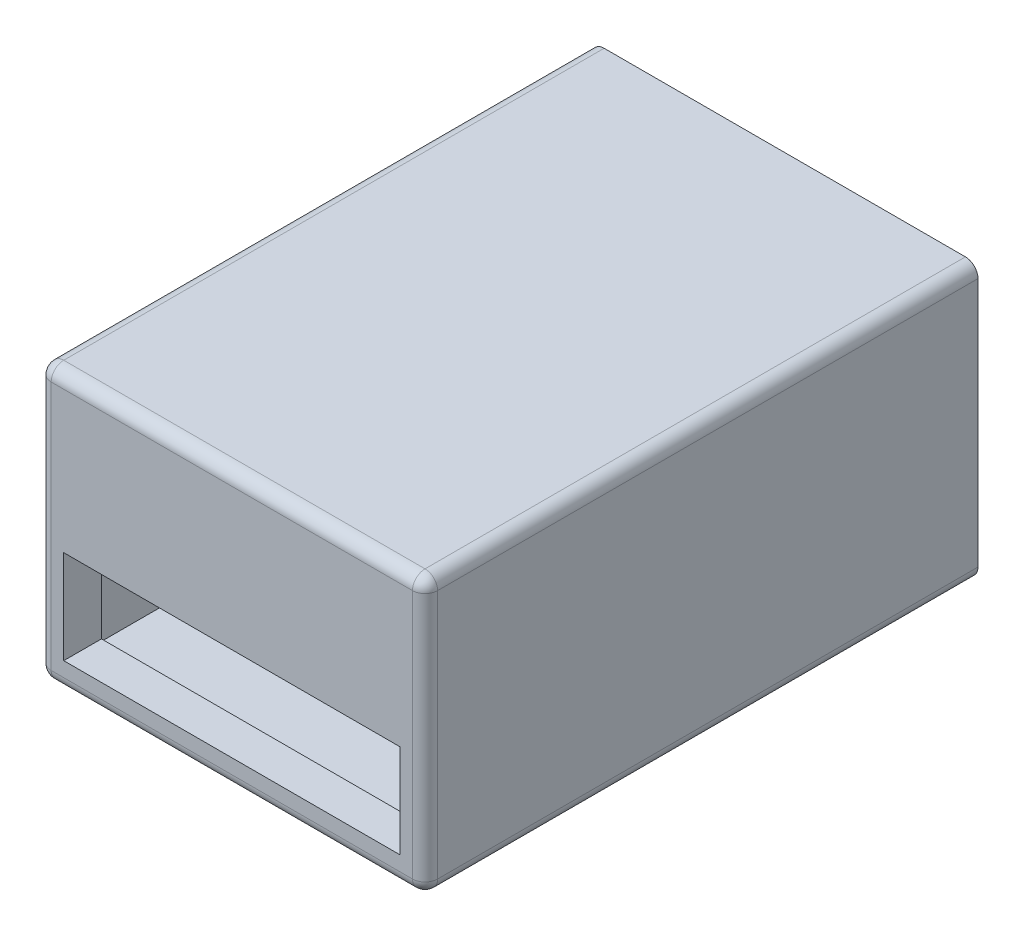
SolidWorks part; units mm, degrees
ref_plane "Plan de face" through (0, 0, 0) normal (0, 0, 1) x (1, 0, 0)
ref_plane "Plan de dessus" through (0, 0, 0) normal (0, 1, 0) x (1, 0, 0)
ref_plane "Plan de droite" through (0, 0, 0) normal (1, 0, 0) x (0, 0, -1)
sketch "Esquisse1" plane through (0, 0, 0) normal (0, 0, 1) x (1, 0, 0)
  line L1 (-31.6005, 34.6263) -> (29.8995, 34.6263)
  line L2 (-31.6005, 34.6263) -> (-31.6005, -9.1237)
  line L3 (-31.6005, -9.1237) -> (29.8995, -9.1237)
  line L4 (29.8995, 34.6263) -> (29.8995, -9.1237)
  dimension "D1" = 43.75
  dimension "D2" = 61.5
extrude "Boss.-Extru.1" add sketch "Esquisse1" along normal blind 88
sketch "Esquisse2" plane through (0, 34.6263, 0) normal (0, 1, 0) x (1, 0, 0)
  line L0 (29.8995, -88) -> (-31.6005, -88) construction
  line L1 (25.8995, -15) -> (-27.6005, -15)
  line L2 (25.8995, -15) -> (25.8995, -84)
  line L3 (25.8995, -84) -> (-27.6005, -84)
  line L4 (-27.6005, -15) -> (-27.6005, -84)
  line L5 (29.8995, -88) -> (29.8995, 0) construction
  dimension "D1" = 69
  dimension "D2" = 53.5
  dimension "D3" = 4
  dimension "D4" = 4
sketch "Esquisse3" plane through (0, 0, 88) normal (0, 0, 1) x (1, 0, 0)
  line L0 (-31.6005, -9.1237) -> (29.8995, -9.1237) construction
  line L1 (-27.6005, -5.1237) -> (25.8995, -5.1237)
  line L3 (-27.6005, 30.6263) -> (25.8995, 30.6263)
  line L17 (-27.6005, -4.7816) -> (25.8995, -4.7816)
  line L21 (-27.6005, -4.7816) -> (-27.6005, 10.1082)
  line L22 (-27.6005, 10.1082) -> (25.8995, 10.1082)
  line L23 (25.8995, 10.1082) -> (25.8995, -4.7816)
  dimension "D1" = 53.5
  dimension "D2" = 35.75
  dimension "D3" = 4
extrude "Enlèv. mat.-Extru.4" cut sketch "Esquisse3" against normal up to next
sketch "Esquisse6" plane through (0, 0, 0) normal (0, 0, -1) x (-1, 0, 0)
  line L7 (29.6005, 32.6263) -> (29.6005, -7.1237)
  line L8 (31.6005, 34.6263) -> (31.6005, -9.1237) construction
  line L10 (-29.8995, 34.6263) -> (31.6005, 34.6263) construction
  line L12 (31.6005, -9.1237) -> (-29.8995, -9.1237) construction
  line L13 (-27.9021, 32.6263) -> (29.6005, 32.6263)
  line L14 (-27.9021, 32.6263) -> (-27.9021, -7.1237)
  line L15 (-27.9021, -7.1237) -> (29.6005, -7.1237)
  line L18 (-29.8995, -9.1237) -> (-29.8995, 34.6263) construction
  dimension "D1" = 2
  dimension "D2" = 2
  dimension "D3" = 2
  dimension "D4" = 2
  dimension "D5" = 2
  dimension "D6" = 1.9974
  dimension "D7" = 2
extrude "Enlèv. mat.-Extru.5" cut sketch "Esquisse6" against normal blind 82
fillet "Congé4" radius 2 8 edges at (-31.6005, 34.6263, 44) (-31.6005, -9.1237, 44) (-31.6005, 12.7513, 88) (-0.8505, -9.1237, 88) (29.8995, -9.1237, 44) (29.8995, 12.7513, 88) (-0.8505, 34.6263, 88) (29.8995, 34.6263, 44)
sketch "Esquisse7" plane through (0, -7.1237, 0) normal (0, 1, 0) x (1, 0, 0)
  line L0 (27.9021, -82) -> (27.9021, 0) construction
  line L1 (27.9021, 0) -> (-29.6005, 0) construction
  circle A0 centre (18.0021, -9.4) radius 1.5
  dimension "D2" = 9.4
  dimension "D1" = 9.9
extrude "Boss.-Extru.2" add sketch "Esquisse7" along normal blind 5.2
sketch "Esquisse8" plane through (0, -7.1237, 0) normal (0, 1, 0) x (1, 0, 0)
  line L0 (-29.6005, -82) -> (-29.6005, 0) construction
  line L1 (27.9021, 0) -> (-29.6005, 0) construction
  circle A0 centre (-9.8505, -9.5) radius 1.5
  dimension "D1" = 19.75
  dimension "D2" = 9.5
extrude "Boss.-Extru.3" add sketch "Esquisse8" along normal blind 5.2
